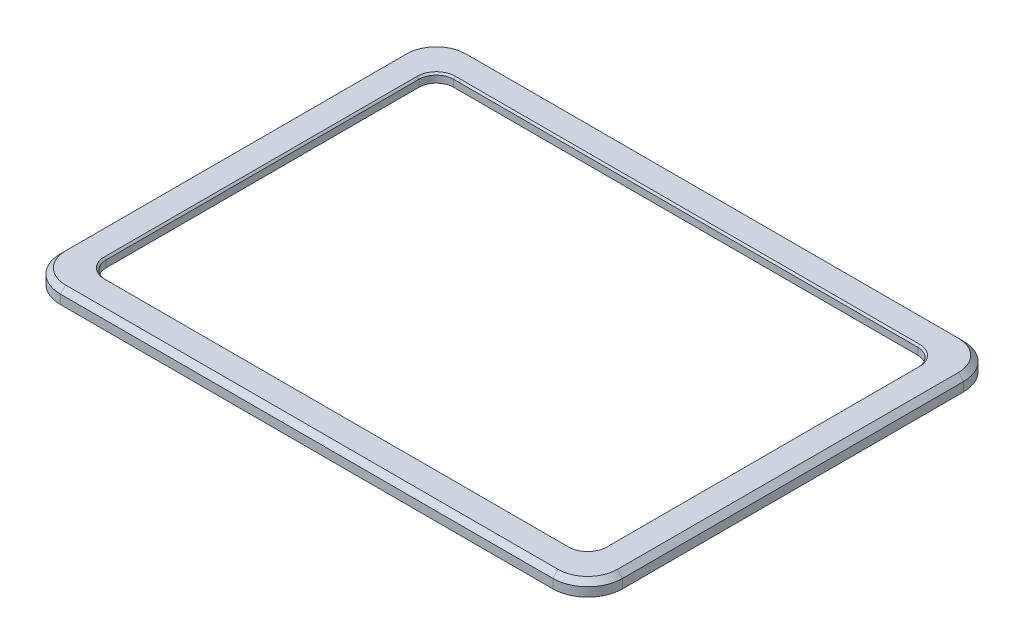
SolidWorks part; units mm, degrees
material "6061 Alloy"
ref_plane "Front Plane" through (0, 0, 0) normal (0, 0, 1) x (1, 0, 0)
ref_plane "Top Plane" through (0, 0, 0) normal (0, 1, 0) x (1, 0, 0)
ref_plane "Right Plane" through (0, 0, 0) normal (1, 0, 0) x (0, 0, -1)
sketch "Sketch1" plane through (0, 0, 0) normal (0, 1, 0) x (1, 0, 0)
  line L0 (-161.5, -118) -> (-161.5, 118)
  line L1 (148.5, -105) -> (-148.5, -105) construction
  line L2 (148.5, -105) -> (148.5, 105) construction
  line L3 (148.5, 105) -> (-148.5, 105) construction
  line L4 (-148.5, -105) -> (-148.5, 105) construction
  line L5 (148.5, -105) -> (-148.5, 105) construction
  line L6 (148.5, 105) -> (-148.5, -105) construction
  line L7 (161.5, 118) -> (-161.5, 118)
  line L8 (161.5, -118) -> (161.5, 118)
  line L9 (161.5, -118) -> (-161.5, -118)
  line L10 (-143.35, -99.85) -> (-143.35, 99.85)
  line L11 (143.35, 99.85) -> (-143.35, 99.85)
  line L12 (143.35, -99.85) -> (143.35, 99.85)
  line L13 (143.35, -99.85) -> (-143.35, -99.85)
  point P0 (0, 0)
  dimension "D1" = 297
  dimension "D2" = 210
  dimension "D3" = 13
  dimension "D4" = 5.15
extrude "Boss-Extrude1" add sketch "Sketch1" along normal blind 5
sketch "Sketch2" plane through (0, 0, 0) normal (0, -1, 0) x (1, 0, 0)
  line L1 (-148.6, 105.1) -> (148.6, 105.1)
  line L2 (-148.6, 105.1) -> (-148.6, -105.1)
  line L3 (-148.6, -105.1) -> (148.6, -105.1)
  line L4 (148.6, 105.1) -> (148.6, -105.1)
  line L5 (-148.6, 105.1) -> (148.6, -105.1) construction
  line L6 (-148.6, -105.1) -> (148.6, 105.1) construction
  line L10 (161.5, 118) -> (-161.5, 118)
  line L11 (-161.5, 118) -> (-161.5, -118)
  line L12 (-161.5, -118) -> (161.5, -118)
  line L13 (161.5, -118) -> (161.5, 118)
  line L14 (161.5, 118) -> (-161.5, 118)
  line L15 (-161.5, 118) -> (-161.5, -118)
  line L16 (-161.5, -118) -> (161.5, -118)
  line L17 (161.5, -118) -> (161.5, 118)
  point P0 (0, 0)
  dimension "D1" = 297.2
  dimension "D2" = 210.2
  dimension "D3" = 0
extrude "Boss-Extrude2" add sketch "Sketch2" along normal blind 3.2
fillet "Fillet1" radius 10 4 edges at (143.35, 2.5, 99.85) (143.35, 2.5, -99.85) (-143.35, 2.5, 99.85) (-143.35, 2.5, -99.85)
fillet "Fillet2" radius 20 4 edges at (-161.5, 0.9, 118) (161.5, 0.9, -118) (161.5, 0.9, 118) (-161.5, 0.9, -118)
hole_wizard "M4 Tapped Hole1" positions "Sketch3" profile "Sketch4" tap size "M4" standard "ISO"
sketch "Sketch3" plane through (0, -3.2, 0) normal (0, -1, 0) x (-1, 0, 0)
  line L0 (0, 0) -> (0, 109) construction
  line L1 (0, 109) -> (66.8, 109) construction
  line L2 (66.8, 109) -> (133.6, 109) construction
  line L4 (148.6, -105.1) -> (148.6, 105.1) construction
  line L5 (0, 105.1) -> (0, 118) construction
  line L6 (148.6, 105.1) -> (-148.6, 105.1) construction
  line L7 (141.5, 118) -> (-141.5, 118) construction
  point P0 (-133.6, 109)
  point P2 (-66.8, 109)
  point P4 (0, 109)
  point P6 (66.8, 109)
  point P8 (133.6, 109)
  dimension "D1" = 15
  dimension "D2" = 9
sketch "Sketch4" plane through (133.6, -3.2, -109) normal (1, 0, 0) x (0, 0, -1)
  line L0 (0, 0) -> (0, 6.9914)
  line L1 (0, 6.9914) -> (1.65, 6)
  line L2 (1.65, 6) -> (1.65, 0)
  line L5 (1.65, 0) -> (0, 0)
  line L10 (0, 6.9914) -> (-1.65, 6) construction
  line L11 (0, -6.35) -> (0, 107.95) construction
  dimension "Tap Drill Dia." = 3.3
  dimension "Tap Drill Depth" = 6
  dimension "Drill Angle" = 118
cosmetic thread "Hole Thread1" parameters "D1"=4, "D2"=4
cosmetic thread "Hole Thread2" parameters "D1"=4, "D2"=4
cosmetic thread "Hole Thread3" parameters "D1"=4, "D2"=4
cosmetic thread "Hole Thread4" parameters "D1"=4, "D2"=4
cosmetic thread "Hole Thread5" parameters "D1"=4, "D2"=4
mirror "Mirror1" about plane through (0, 0, 0) normal (0, 0, 1) of "M4 Tapped Hole1"
cosmetic thread "Hole Thread6" parameters "D1"=4, "D2"=4
cosmetic thread "Hole Thread7" parameters "D1"=4, "D2"=4
cosmetic thread "Hole Thread8" parameters "D1"=4, "D2"=4
cosmetic thread "Hole Thread9" parameters "D1"=4, "D2"=4
cosmetic thread "Hole Thread10" parameters "D1"=4, "D2"=4
hole_wizard "M4 Tapped Hole2" positions "Sketch5" profile "Sketch6" tap size "M4" standard "ISO"
sketch "Sketch5" plane through (0, -3.2, 0) normal (0, -1, 0) x (-1, 0, 0)
  line L0 (0, 0) -> (-152.5, 0) construction
  line L2 (-148.6, 0) -> (-161.5, 0) construction
  line L3 (-148.6, 105.1) -> (-148.6, -105.1) construction
  line L4 (-161.5, 98) -> (-161.5, -98) construction
  line L6 (-152.5, 0) -> (-152.5, 45.05) construction
  line L7 (-152.5, 45.05) -> (-152.5, 90.1) construction
  line L9 (148.6, 105.1) -> (-148.6, 105.1) construction
  point P0 (-152.5, 90.1)
  point P2 (-152.5, 45.05)
  point P4 (-152.5, 0)
  point P28 (-152.5, -45.05)
  point P29 (-152.5, -90.1)
  dimension "D1" = 15
  dimension "D2" = 9
sketch "Sketch6" plane through (152.5, -3.2, -90.1) normal (1, 0, 0) x (0, 0, -1)
  line L0 (0, 0) -> (0, 7.0914)
  line L1 (0, 7.0914) -> (1.65, 6.1)
  line L2 (1.65, 6.1) -> (1.65, 0)
  line L5 (1.65, 0) -> (0, 0)
  line L10 (0, 7.0914) -> (-1.65, 6.1) construction
  line L11 (0, -6.35) -> (0, 107.95) construction
  dimension "Tap Drill Dia." = 3.3
  dimension "Tap Drill Depth" = 6.1
  dimension "Drill Angle" = 118
cosmetic thread "Hole Thread11" parameters "D1"=4, "D2"=4
cosmetic thread "Hole Thread12" parameters "D1"=4, "D2"=4
cosmetic thread "Hole Thread13" parameters "D1"=4, "D2"=4
cosmetic thread "Hole Thread14" parameters "D1"=4, "D2"=4
cosmetic thread "Hole Thread15" parameters "D1"=4, "D2"=4
mirror "Mirror2" about plane through (0, 0, 0) normal (1, 0, 0) of "M4 Tapped Hole2"
cosmetic thread "Hole Thread16" parameters "D1"=4, "D2"=4
cosmetic thread "Hole Thread17" parameters "D1"=4, "D2"=4
cosmetic thread "Hole Thread18" parameters "D1"=4, "D2"=4
cosmetic thread "Hole Thread19" parameters "D1"=4, "D2"=4
cosmetic thread "Hole Thread20" parameters "D1"=4, "D2"=4
chamfer "Chamfer2" distance 3 angle 45 8 edges at (-161.5, 5, 0) (-155.6421, 5, 112.1421) (-155.6421, 5, -112.1421) (0, 5, 118) (0, 5, -118) (155.6421, 5, 112.1421) (155.6421, 5, -112.1421) (161.5, 5, 0)
sketch "Sketch7" plane through (0, -3.2, 0) normal (0, -1, 0) x (1, 0, 0)
  line L0 (0, 0) -> (0, -34.1409) construction
  line L1 (0, 0) -> (-25.5067, 0) construction
  line L2 (-148.6, -105.1) -> (148.6, -105.1) construction
  line L3 (148.6, -105.1) -> (148.6, 105.1) construction
  circle A0 centre (147.3, -103.8) radius 3
  circle A1 centre (-147.3, -103.8) radius 3
  circle A2 centre (-147.3, 103.8) radius 3
  circle A3 centre (147.3, 103.8) radius 3
  dimension "D1" = 6
  dimension "D2" = 1.3
  dimension "D3" = 1.3
extrude "Cut-Extrude1" cut sketch "Sketch7" against normal up to surface (3.2 mm away) up to face at (0, 0, 0)
fillet "Fillet3" radius 10 8 edges at (148.6, -1.6, -101.0963) (-144.5963, -1.6, -105.1) (-148.6, -1.6, -101.0963) (-148.6, -1.6, 101.0963) (-144.5963, -1.6, 105.1) (144.5963, -1.6, 105.1) (148.6, -1.6, 101.0963) (144.5963, -1.6, -105.1)
chamfer "Chamfer3" distance 1 angle 45 8 edges at (143.35, 5, 0) (140.4211, 5, -96.9211) (140.4211, 5, 96.9211) (0, 5, -99.85) (0, 5, 99.85) (-140.4211, 5, -96.9211) (-140.4211, 5, 96.9211) (-143.35, 5, 0)
sketch "Sketch8" plane through (0, 0, 0) normal (0, -1, 0) x (1, 0, 0)
  line L20 (148.6, -89.85) -> (148.6, 89.85)
  line L21 (133.35, 105.1) -> (-133.35, 105.1)
  line L22 (-148.6, 89.85) -> (-148.6, -89.85)
  line L23 (-133.35, -105.1) -> (133.35, -105.1)
  line L24 (133.35, 101.85) -> (-133.35, 101.85)
  line L25 (-145.35, 89.85) -> (-145.35, -89.85)
  line L26 (-133.35, -101.85) -> (133.35, -101.85)
  line L27 (145.35, -89.85) -> (145.35, 89.85)
  line L28 (133.35, 101.85) -> (-133.35, 101.85)
  line L29 (-145.35, 89.85) -> (-145.35, -89.85)
  line L30 (-133.35, -101.85) -> (133.35, -101.85)
  line L31 (145.35, -89.85) -> (145.35, 89.85)
  arc A16 (133.35, -105.1) -> (148.6, -89.85) centre (133.35, -89.85) ccw
  arc A17 (148.6, 89.85) -> (133.35, 105.1) centre (133.35, 89.85) ccw
  arc A18 (-133.35, 105.1) -> (-148.6, 89.85) centre (-133.35, 89.85) ccw
  arc A19 (-148.6, -89.85) -> (-133.35, -105.1) centre (-133.35, -89.85) ccw
  arc A20 (145.35, 89.85) -> (133.35, 101.85) centre (133.35, 89.85) ccw
  arc A21 (-133.35, 101.85) -> (-145.35, 89.85) centre (-133.35, 89.85) ccw
  arc A22 (-145.35, -89.85) -> (-133.35, -101.85) centre (-133.35, -89.85) ccw
  arc A23 (133.35, -101.85) -> (145.35, -89.85) centre (133.35, -89.85) ccw
  arc A24 (145.35, 89.85) -> (133.35, 101.85) centre (133.35, 89.85) ccw
  arc A25 (-133.35, 101.85) -> (-145.35, 89.85) centre (-133.35, 89.85) ccw
  arc A26 (-145.35, -89.85) -> (-133.35, -101.85) centre (-133.35, -89.85) ccw
  arc A27 (133.35, -101.85) -> (145.35, -89.85) centre (133.35, -89.85) ccw
  dimension "D1" = 2
  dimension "D2" = 3.25
extrude "Cut-Extrude2" cut sketch "Sketch8" against normal blind 2
sketch "Sketch9" plane through (0, -3.2, 0) normal (0, -1, 0) x (1, 0, 0)
  line L20 (156.25, -98) -> (156.25, 98)
  line L21 (141.5, 112.75) -> (-141.5, 112.75)
  line L22 (-156.25, 98) -> (-156.25, -98)
  line L23 (-141.5, -112.75) -> (141.5, -112.75)
  line L24 (141.5, 116) -> (-141.5, 116)
  line L25 (-159.5, 98) -> (-159.5, -98)
  line L26 (-141.5, -116) -> (141.5, -116)
  line L27 (159.5, -98) -> (159.5, 98)
  line L28 (141.5, 116) -> (-141.5, 116)
  line L29 (-159.5, 98) -> (-159.5, -98)
  line L30 (-141.5, -116) -> (141.5, -116)
  line L31 (159.5, -98) -> (159.5, 98)
  arc A16 (141.5, -112.75) -> (156.25, -98) centre (141.5, -98) ccw
  arc A17 (156.25, 98) -> (141.5, 112.75) centre (141.5, 98) ccw
  arc A18 (-141.5, 112.75) -> (-156.25, 98) centre (-141.5, 98) ccw
  arc A19 (-156.25, -98) -> (-141.5, -112.75) centre (-141.5, -98) ccw
  arc A20 (159.5, 98) -> (141.5, 116) centre (141.5, 98) ccw
  arc A21 (-141.5, 116) -> (-159.5, 98) centre (-141.5, 98) ccw
  arc A22 (-159.5, -98) -> (-141.5, -116) centre (-141.5, -98) ccw
  arc A23 (141.5, -116) -> (159.5, -98) centre (141.5, -98) ccw
  arc A24 (159.5, 98) -> (141.5, 116) centre (141.5, 98) ccw
  arc A25 (-141.5, 116) -> (-159.5, 98) centre (-141.5, 98) ccw
  arc A26 (-159.5, -98) -> (-141.5, -116) centre (-141.5, -98) ccw
  arc A27 (141.5, -116) -> (159.5, -98) centre (141.5, -98) ccw
  dimension "D1" = 2
  dimension "D2" = 3.25
extrude "Cut-Extrude3" cut sketch "Sketch9" against normal blind 2
